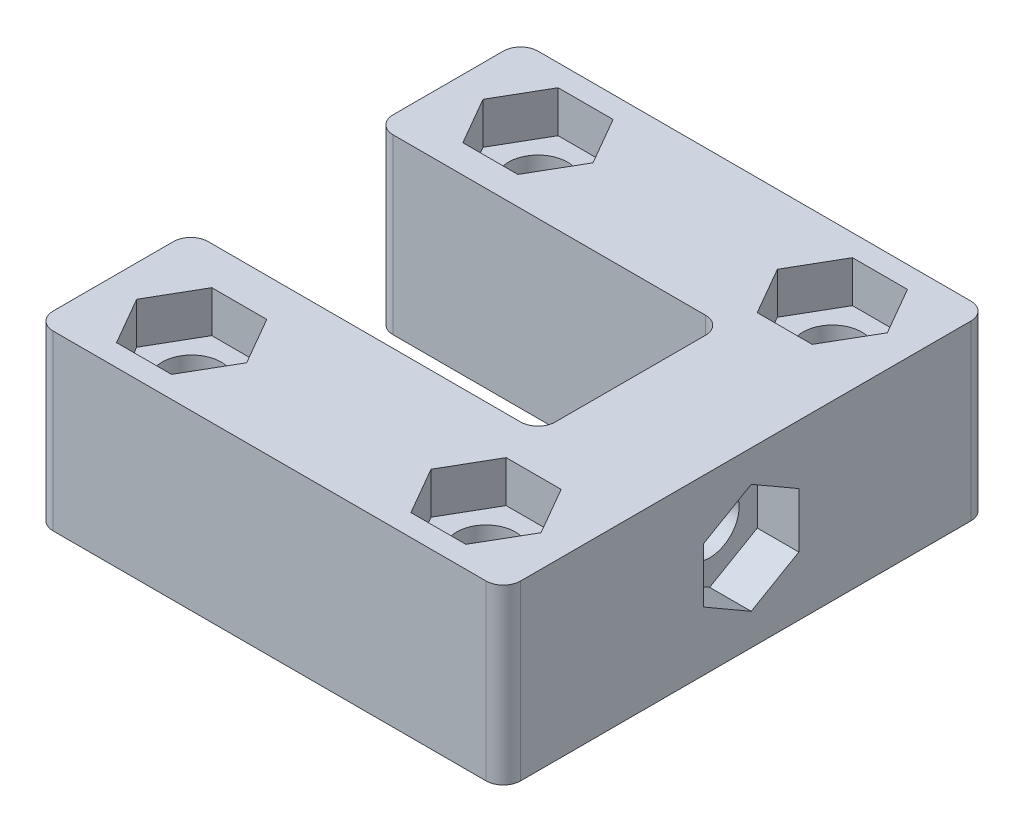
SolidWorks part; units mm, degrees
material "ABS"
ref_plane "Front Plane" through (0, 0, 0) normal (0, 0, 1) x (1, 0, 0)
ref_plane "Top Plane" through (0, 0, 0) normal (0, 1, 0) x (1, 0, 0)
ref_plane "Right Plane" through (0, 0, 0) normal (1, 0, 0) x (0, 0, -1)
sketch "Sketch1" plane through (0, 0, 0) normal (0, 1, 0) x (1, 0, 0)
  line L0 (20, 9) -> (20, 18) construction
  line L1 (0, 0) -> (27, 0)
  line L2 (0, 0) -> (0, 28)
  line L3 (0, 28) -> (27, 28)
  line L4 (27, 0) -> (27, 28)
  line L7 (0, 14) -> (27, 14) construction
  line L8 (4.5, 14) -> (15.5, 14) construction
  dimension "D2" = 7
extrude "Boss-Extrude1" add sketch "Sketch1" along normal blind 10
ref_plane "Plane1" through (0, 5, 0) normal (0, 1, 0) x (1, 0, 0)
sketch "Sketch2" plane through (0, 10, 0) normal (0, 1, 0) x (1, 0, 0)
  line L0 (0, 28) -> (0, 0) construction
  line L1 (0, 8.95) -> (20.05, 8.95)
  line L2 (0, 8.95) -> (0, 19.63)
  line L3 (0, 19.63) -> (20.05, 19.63)
  line L4 (20.05, 8.95) -> (20.05, 19.63)
  line L5 (0, 9) -> (20, 9) construction
  line L7 (15.5, 19.63) -> (4.5, 19.63) construction
  line L8 (20, 9) -> (20, 18) construction
  dimension "D1" = 0.05
  dimension "D2" = 0.05
extrude "Cut-Extrude1" cut sketch "Sketch2" against normal through all
hole_wizard "M3 Clearance Hole1" positions "Sketch4" profile "Sketch3" hole size "M3" standard "ANSI Metric" end condition through all
sketch "Sketch4" plane through (27, 0, 0) normal (1, 0, 0) x (0, 0, -1)
  circle A1 centre (14.315, 5) radius 1.7 construction
  point P0 (14.315, 5)
sketch "Sketch3" plane through (27, 5, -14.315) normal (0, 1, 0) x (0, 0, -1)
  line L0 (0, 0) -> (0, 27)
  line L1 (0, 27) -> (1.7, 27)
  line L2 (1.7, 27) -> (1.7, 0)
  line L5 (1.7, 0) -> (0, 0)
  line L11 (0, -6.35) -> (0, 107.95) construction
  dimension "Thru Hole Dia." = 3.4
  dimension "Thru Hole Depth" = 27
hole_wizard "M3 Clearance Hole2" positions "Sketch6" profile "Sketch5" hole size "M3" standard "ANSI Metric" end condition through all
sketch "Sketch6" plane through (0, 10, 0) normal (0, 1, 0) x (1, 0, 0)
  line L0 (5, 24) -> (5, 4) construction
  line L1 (5, 4) -> (22, 4) construction
  line L2 (22, 4) -> (22, 24) construction
  line L3 (22, 24) -> (5, 24) construction
  line L5 (22, 24) -> (22, 28) construction
  line L6 (27, 28) -> (0, 28) construction
  line L8 (22, 24) -> (27, 24) construction
  line L9 (27, 0) -> (27, 28) construction
  line L12 (5, 24) -> (5, 28) construction
  line L14 (5, 24) -> (0, 24) construction
  line L18 (0, 28) -> (0, 19.63) construction
  line L19 (5, 4) -> (5, 0) construction
  line L20 (0, 0) -> (27, 0) construction
  line L22 (0, 4) -> (5, 4) construction
  line L23 (0, 8.95) -> (0, 0) construction
  line L25 (22, 4) -> (27, 4) construction
  line L27 (22, 4) -> (22, 0) construction
  point P0 (5, 24)
  point P2 (22, 24)
  point P4 (22, 4)
  point P6 (5, 4)
  dimension "D1" = 4
  dimension "D2" = 5
  dimension "D3" = 5
sketch "Sketch5" plane through (5, 10, -24) normal (1, 0, 0) x (0, 0, 1)
  line L0 (0, 0) -> (0, 10)
  line L1 (0, 10) -> (1.7, 10)
  line L2 (1.7, 10) -> (1.7, 0)
  line L5 (1.7, 0) -> (0, 0)
  line L11 (0, -6.35) -> (0, 107.95) construction
  dimension "Thru Hole Dia." = 3.4
  dimension "Thru Hole Depth" = 10
sketch "Sketch7" plane through (0, 10, 0) normal (0, 1, 0) x (1, 0, 0)
  line L1 (6.5877, 1.25) -> (8.1754, 4)
  line L2 (8.1754, 4) -> (6.5877, 6.75)
  line L3 (6.5877, 6.75) -> (3.4123, 6.75)
  line L4 (3.4123, 6.75) -> (1.8246, 4)
  line L5 (1.8246, 4) -> (3.4123, 1.25)
  line L6 (3.4123, 1.25) -> (6.5877, 1.25)
  line L7 (23.5877, 1.25) -> (25.1754, 4)
  line L8 (25.1754, 4) -> (23.5877, 6.75)
  line L9 (23.5877, 6.75) -> (20.4123, 6.75)
  line L10 (20.4123, 6.75) -> (18.8246, 4)
  line L11 (18.8246, 4) -> (20.4123, 1.25)
  line L12 (20.4123, 1.25) -> (23.5877, 1.25)
  line L13 (23.5877, 21.25) -> (25.1754, 24)
  line L14 (25.1754, 24) -> (23.5877, 26.75)
  line L15 (23.5877, 26.75) -> (20.4123, 26.75)
  line L16 (20.4123, 26.75) -> (18.8246, 24)
  line L17 (18.8246, 24) -> (20.4123, 21.25)
  line L18 (20.4123, 21.25) -> (23.5877, 21.25)
  line L19 (6.5877, 21.25) -> (8.1754, 24)
  line L20 (8.1754, 24) -> (6.5877, 26.75)
  line L21 (6.5877, 26.75) -> (3.4123, 26.75)
  line L22 (3.4123, 26.75) -> (1.8246, 24)
  line L23 (1.8246, 24) -> (3.4123, 21.25)
  line L24 (3.4123, 21.25) -> (6.5877, 21.25)
  circle A0 centre (5, 4) radius 2.75 construction
  circle A1 centre (22, 4) radius 2.75 construction
  circle A2 centre (22, 24) radius 2.75 construction
  circle A3 centre (5, 24) radius 2.75 construction
extrude "Cut-Extrude2" cut sketch "Sketch7" against normal up to surface (2.4 mm away)
mirror "Mirror1" about plane through (0, 5, 0) normal (0, 1, 0) of "Cut-Extrude2"
fillet "Fillet1" radius 1 8 edges at (27, 5, -28) (27, 5, 0) (0, 5, 0) (0, 5, -8.95) (20.05, 5, -8.95) (20.05, 5, -19.63) (0, 5, -19.63) (0, 5, -28)
sketch "Sketch12" plane through (27, 0, 0) normal (1, 0, 0) x (0, 0, -1)
  line L1 (14.315, 1.8246) -> (17.065, 3.4123)
  line L2 (17.065, 3.4123) -> (17.065, 6.5877)
  line L3 (17.065, 6.5877) -> (14.315, 8.1754)
  line L4 (14.315, 8.1754) -> (11.565, 6.5877)
  line L5 (11.565, 6.5877) -> (11.565, 3.4123)
  line L6 (11.565, 3.4123) -> (14.315, 1.8246)
  circle A0 centre (14.315, 5) radius 2.75 construction
extrude "Cut-Extrude8" cut sketch "Sketch12" against normal up to surface (2.4 mm away)
